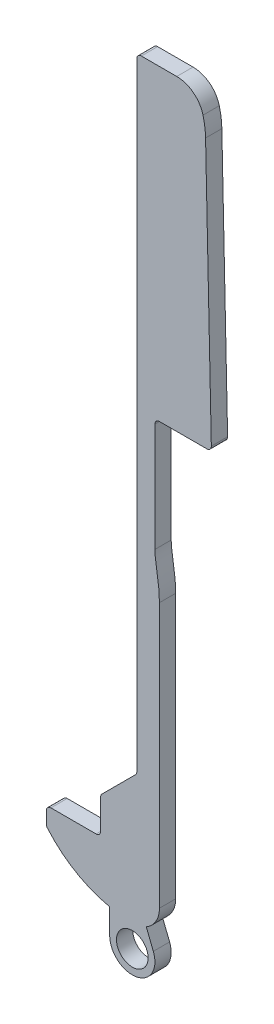
SolidWorks part; units mm, degrees
material "1060 Alloy"
ref_plane "Front Plane" through (0, 0, 0) normal (0, 0, 1) x (1, 0, 0)
ref_plane "Top Plane" through (0, 0, 0) normal (0, 1, 0) x (1, 0, 0)
ref_plane "Right Plane" through (0, 0, 0) normal (1, 0, 0) x (0, 0, -1)
sketch "Sketch1" plane through (0, 0, 0) normal (0, 0, 1) x (1, 0, 0)
  line L0 (0, 0) -> (0, 83.5) construction
  line L1 (0, 83.5) -> (18.25, 83.5) construction
  line L2 (18.25, 83.5) -> (18.25, 0) construction
  line L3 (18.25, 0) -> (0, 0) construction
  line L4 (0, 4.5) -> (0, 6.5)
  line L5 (0, 6.5) -> (6, 6.5)
  line L6 (6, 6.5) -> (6, 10.5)
  line L7 (6, 10.5) -> (10, 14.5)
  line L8 (10, 14.5) -> (10, 83.5)
  line L9 (18.25, 49.5) -> (17.602, 79.1992)
  line L10 (18.25, 49.5) -> (12, 49.5)
  line L11 (12, 49.5) -> (12, 37)
  line L12 (12.5, 32.15) -> (12.5, 2.89)
  line L13 (12, 35.4908) -> (12, 38.5096) construction
  line L14 (12.5, 30.5478) -> (12.5, 33.7533) construction
  line L15 (10, 83.5) -> (16.4, 83.5)
  arc A0 (17.602, 79.1992) -> (16.4, 83.5) centre (8.6041, 79.0029) ccw
  arc A1 (12.5, 2.89) -> (9.61, 0) centre (9.61, 2.89) cw
  arc A2 (9.61, 0) -> (0, 4.5) centre (9.61, 12.5113) cw
  spline S0 degree 3 poles (12, 37) (12, 35.7422) (12.5, 34.1535) (12.5, 32.15) knots 0 0 0 0 1 1 1 1
  point P3 (0, 4.5)
  point P6 (0, 6.5)
  point P7 (16.4, 83.5)
  point P8 (18.25, 49.5)
  dimension "D12" = 9
  dimension "D1" = 83.5
  dimension "D2" = 18.25
  dimension "D3" = 4.5
  dimension "D4" = 2
  dimension "D5" = 34
  dimension "D6" = 1.85
  dimension "D7" = 6
  dimension "D8" = 4
  dimension "D9" = 45
  dimension "D10" = 1.25
  dimension "D11" = 4
  dimension "D13" = 6.25
  dimension "D14" = 12.5
  dimension "D15" = 29.26
  dimension "D16" = 2.5
  dimension "D17" = 4.85
extrude "Boss-Extrude1" add sketch "Sketch1" along normal blind 1.8
fillet "Fillet1" radius 0.5 8 edges at (10, 83.5, 0.9) (0, 4.5, 0.9) (0, 6.5, 0.9) (6, 6.5, 0.9) (10, 14.5, 0.9) (6, 10.5, 0.9) (12, 49.5, 0.9) (18.25, 49.5, 0.9)
sketch "Sketch2" plane through (0, 0, 0) normal (0, 0, 1) x (1, 0, 0)
  line L0 (7, -2.4996) -> (7, 0.5004)
  line L1 (7, 0.5004) -> (11, 0.5004)
  line L2 (11, 0.5004) -> (11.824, -1.5783)
  line L3 (12.5, 2.89) -> (12.5, 32.15) construction
  arc A0 (7, -2.4996) -> (11.824, -1.5783) centre (9.5, -2.4996) ccw
  arc A1 (0.1208, 4.3573) -> (9.61, 0) centre (9.61, 12.5113) ccw construction
  circle A2 centre (9.5, -2.4996) radius 1.75
  dimension "D1" = 5
  dimension "D3" = 3
  dimension "D2" = 3
  dimension "D4" = 4
extrude "Boss-Extrude3" add sketch "Sketch2" along normal blind 1.8
fillet "Fillet2" radius 3 1 edges at (16.4, 83.5, 0.9)
